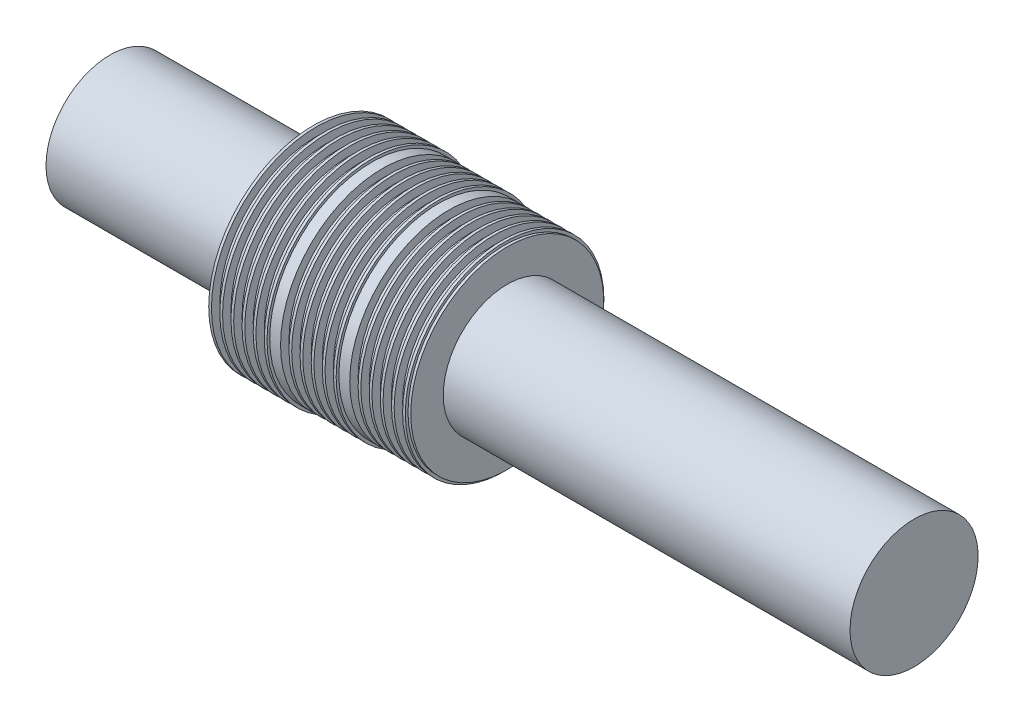
SolidWorks part; units mm, degrees
ref_plane "Front Plane" through (0, 0, 0) normal (0, 0, 1) x (1, 0, 0)
ref_plane "Top Plane" through (0, 0, 0) normal (0, 1, 0) x (1, 0, 0)
ref_plane "Right Plane" through (0, 0, 0) normal (1, 0, 0) x (0, 0, -1)
sketch "Sketch1" plane through (0, 0, 0) normal (0, 0, 1) x (1, 0, 0)
  line L89 (19.05, 9.81) -> (19.304, 9.81)
  line L90 (19.304, 9.81) -> (19.304, 9.0226)
  line L91 (19.304, 9.0226) -> (20.0914, 9.0226)
  line L92 (20.0914, 9.0226) -> (20.0914, 9.81)
  line L93 (20.0914, 9.81) -> (20.3454, 9.81)
  line L94 (20.3454, 9.81) -> (20.3454, 9.0226)
  line L95 (20.3454, 9.0226) -> (21.1328, 9.0226)
  line L96 (21.1328, 9.0226) -> (21.1328, 9.81)
  line L97 (21.1328, 9.81) -> (21.3868, 9.81)
  line L98 (21.3868, 9.81) -> (21.3868, 9.0226)
  line L99 (21.3868, 9.0226) -> (22.1742, 9.0226)
  line L100 (22.1742, 9.0226) -> (22.1742, 9.81)
  line L101 (22.1742, 9.81) -> (22.4282, 9.81)
  line L102 (22.4282, 9.81) -> (22.4282, 9.0226)
  line L103 (22.4282, 9.0226) -> (23.2156, 9.0226)
  line L104 (23.2156, 9.0226) -> (23.2156, 9.81)
  line L105 (23.2156, 9.81) -> (23.4696, 9.81)
  line L106 (23.4696, 9.81) -> (23.4696, 9.0226)
  line L107 (23.4696, 9.0226) -> (24.257, 9.0226)
  line L108 (24.257, 9.0226) -> (24.257, 9.81)
  line L109 (24.257, 9.81) -> (24.511, 9.81)
  line L110 (24.511, 9.81) -> (24.511, 9.556)
  line L111 (24.511, 9.556) -> (25.527, 9.556)
  line L112 (25.527, 9.556) -> (25.527, 8.7686)
  line L113 (25.527, 8.7686) -> (26.3144, 8.7686)
  line L114 (26.3144, 8.7686) -> (26.3144, 9.556)
  line L115 (26.3144, 9.556) -> (26.5684, 9.556)
  line L116 (26.5684, 9.556) -> (26.5684, 8.7686)
  line L117 (26.5684, 8.7686) -> (27.3558, 8.7686)
  line L118 (27.3558, 8.7686) -> (27.3558, 9.556)
  line L119 (27.3558, 9.556) -> (27.6098, 9.556)
  line L120 (27.6098, 9.556) -> (27.6098, 8.7686)
  line L121 (27.6098, 8.7686) -> (28.3972, 8.7686)
  line L122 (28.3972, 8.7686) -> (28.3972, 9.556)
  line L123 (28.3972, 9.556) -> (28.6512, 9.556)
  line L124 (28.6512, 9.556) -> (28.6512, 8.7686)
  line L125 (28.6512, 8.7686) -> (29.4386, 8.7686)
  line L126 (29.4386, 8.7686) -> (29.4386, 9.556)
  line L127 (29.4386, 9.556) -> (29.6926, 9.556)
  line L128 (29.6926, 9.556) -> (29.6926, 8.7686)
  line L129 (29.6926, 8.7686) -> (30.48, 8.7686)
  line L130 (30.48, 8.7686) -> (30.48, 9.556)
  line L131 (30.48, 9.556) -> (30.734, 9.556)
  line L132 (30.734, 9.556) -> (30.734, 9.302)
  line L133 (30.734, 9.302) -> (31.75, 9.302)
  line L134 (31.75, 9.302) -> (31.75, 8.5146)
  line L135 (31.75, 8.5146) -> (32.5374, 8.5146)
  line L136 (32.5374, 8.5146) -> (32.5374, 9.302)
  line L137 (32.5374, 9.302) -> (32.7914, 9.302)
  line L138 (32.7914, 9.302) -> (32.7914, 8.5146)
  line L139 (32.7914, 8.5146) -> (33.5788, 8.5146)
  line L140 (33.5788, 8.5146) -> (33.5788, 9.302)
  line L141 (33.5788, 9.302) -> (33.8328, 9.302)
  line L142 (33.8328, 9.302) -> (33.8328, 8.5146)
  line L143 (33.8328, 8.5146) -> (34.6202, 8.5146)
  line L144 (34.6202, 8.5146) -> (34.6202, 9.302)
  line L145 (34.6202, 9.302) -> (34.8742, 9.302)
  line L146 (34.8742, 9.302) -> (34.8742, 8.5146)
  line L147 (34.8742, 8.5146) -> (35.6616, 8.5146)
  line L148 (35.6616, 8.5146) -> (35.6616, 9.302)
  line L149 (35.6616, 9.302) -> (35.9156, 9.302)
  line L150 (35.9156, 9.302) -> (35.9156, 8.5146)
  line L151 (35.9156, 8.5146) -> (36.703, 8.5146)
  line L152 (36.703, 8.5146) -> (36.703, 9.302)
  line L153 (36.703, 9.302) -> (36.957, 9.302)
  line L154 (36.957, 9.302) -> (36.957, 9.048)
  line L155 (36.957, 9.048) -> (37.211, 9.048)
  line L156 (19.05, 6) -> (0, 6)
  line L157 (0, 6) -> (0, 0)
  line L158 (0, 0) -> (61.976, 0)
  line L159 (37.211, 6) -> (37.211, 9.048)
  line L162 (37.211, 6) -> (75.311, 6)
  line L163 (75.311, 6) -> (75.311, 0)
  line L164 (75.311, 0) -> (61.976, 0)
  line L165 (19.05, 9.81) -> (19.05, 6)
  point P6 (56.261, 6)
  dimension "D1" = 6
  dimension "D8" = 0.254
  dimension "D6" = 0.254
  dimension "D10" = 6
  dimension "D11" = 38.1
  dimension "D7" = 19.05
  dimension "D3" = 0.254
  dimension "D5" = 0.7874
  dimension "D4" = 0.7874
  dimension "D9" = 1.016
  dimension "D2" = 9.81
  dimension "D12" = 0.254
revolve "Revolve1" add sketch "Sketch1" angle 360 about L158
equation "\"kero_radius\"=0.334in"
equation "\"D1@Sketch1\"=\"lox_radius\""
equation "\"lox_radius\"=0.23622in"
equation "\"Cavity_width\"=0.031in"
equation "\"tooth_width\"=0.01in"
equation "\"cavity_depth\"=0.031in"
equation "\"seal_step\"=0.01in"
equation "\"purge_length\"=0.04in"
equation "\"D6@Sketch1\"=\"seal_step\""
equation "\"D10@Sketch1\"=\"lox_radius\""
equation "\"bearing_radius\"= 0.629921"
equation "\"bearing_width\"=0.393701"
equation "\"insert_radius\" = 0.6in"
equation "\"recycle_groove width\" = 0.06in"
equation "\"recycle_groove_depth\" = 0.06in"
equation "\"N2_purge_width\"= .06in"
equation "\"N2_purge_depth\"= .06in"
equation "\"drain_width\"= .06in"
equation "\"drain_depth\"= .06in"
equation "\"radial_clearance\"= .002in"
equation "\"IPS_flange_width\"= .25in"
equation "\"IPS_flange_radius\" = 1.4in"
equation "\"IPS_LOX_male_radius\"= .9in"
equation "\"IPS_Kero_male_radius\" = .9in"
equation "\"IPS_radius\"= .95in"
equation "\"InsertLength\"= 1in"
equation "\"D3@Sketch1\"=\"tooth_width\""
equation "\"D5@Sketch1\"=\"cavity_depth\""
equation "\"D4@Sketch1\"=\"Cavity_width\""
equation "\"D9@Sketch1\"=\"purge_length\""
equation "\"D2@Sketch1\"=\"lox_radius\"+.15"
equation "\"D12@Sketch1\"=\"tooth_width\""
